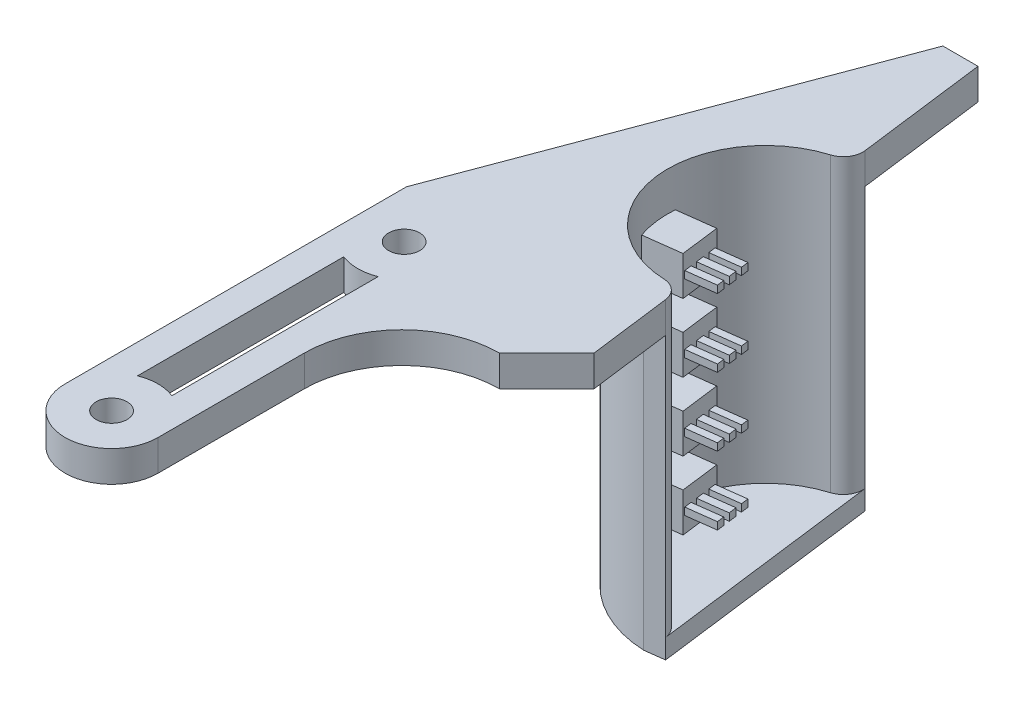
SolidWorks part; units mm, degrees
ref_plane "Alzado" through (0, 0, 0) normal (0, 0, 1) x (1, 0, 0)
ref_plane "Planta" through (0, 0, 0) normal (0, 1, 0) x (1, 0, 0)
ref_plane "Vista lateral" through (0, 0, 0) normal (1, 0, 0) x (0, 0, -1)
sketch "Croquis1" plane through (0, 0, 0) normal (0, 1, 0) x (1, 0, 0)
  line L0 (-12.5, 40) -> (12.5, -40) construction
  line L1 (-12.5, 40) -> (12.5, 40) construction
  line L2 (-12.5, 40) -> (-12.5, -40) construction
  line L3 (-12.5, -40) -> (12.5, -40) construction
  line L4 (12.5, 40) -> (12.5, -40) construction
  line L5 (-12.5, 0) -> (-12.5, -40)
  line L6 (-12.5, -40) -> (-2.975, -40)
  line L7 (-2.975, -40) -> (-2.975, -20)
  line L8 (7.025, -10) -> (12.5, -10)
  line L9 (12.5, -10) -> (12.5, 40)
  line L10 (12.5, 40) -> (2.5, 40)
  line L11 (2.5, 40) -> (-12.5, 0)
  circle A0 centre (-7.7375, -5) radius 1.5875
  circle A1 centre (-7.7375, -35) radius 1.5875
  arc A2 (-2.975, -20) -> (7.025, -10) centre (7.025, -20) cw
  dimension "D5" = 3.175
  dimension "D6" = 3.175
  dimension "D12" = 10
  dimension "D1" = 25
  dimension "D2" = 80
  dimension "D3" = 9.525
  dimension "D4" = 30
  dimension "D7" = 4.7625
  dimension "D8" = 5
  dimension "D9" = 10
  dimension "D10" = 40
  dimension "D11" = 50
extrude "Saliente-Extruir1" add sketch "Croquis1" along normal blind 3.175
sketch "Croquis2" plane through (0, 3.175, 0) normal (0, 1, 0) x (1, 0, 0)
  line L0 (12.5, -10) -> (6.1, 40)
  line L1 (12.5, 40) -> (2.5, 40) construction
  line L2 (6.1, 40) -> (12.5, 40)
  line L3 (12.5, 40) -> (12.5, -10)
  dimension "D1" = 6.4
extrude "Cortar-Extruir1" cut sketch "Croquis2" against normal blind 3.175
sketch "Croquis3" plane through (0, 3.175, 0) normal (0, 1, 0) x (1, 0, 0)
  line L1 (-2.975, -40) -> (-2.975, -20) construction
  line L2 (-12.5, -35) -> (-12.5, -40)
  line L3 (-12.5, -40) -> (-2.975, -40)
  line L4 (-2.975, -40) -> (-2.975, -35)
  line L5 (-9.5, -9.4271) -> (-9.5, -30.5756)
  line L6 (-5.975, -14.8038) -> (-5.975, -30.5756)
  line L7 (-12.5, 0) -> (-12.5, -40) construction
  line L8 (-5.975, -14.8038) -> (-5.975, -9.4271)
  line L22 (7.025, -6) -> (7.9554, -6)
  line L23 (7.9554, -6) -> (3.2646, 30.6468)
  line L24 (3.2646, 30.6468) -> (-8.5, -0.7253)
  line L25 (-8.5, -0.7253) -> (-8.5, -36)
  line L26 (-8.5, -36) -> (-6.975, -36)
  line L27 (-6.975, -36) -> (-6.975, -20)
  line L28 (7.025, -6) -> (7.9554, -6)
  arc A2 (-9.5, -9.4271) -> (-5.975, -9.4271) centre (-7.7375, -5) ccw
  arc A3 (-12.5, -35) -> (-2.975, -35) centre (-7.7375, -35) ccw
  arc A4 (-5.975, -30.5756) -> (-9.5, -30.5756) centre (-7.7375, -35) ccw
  arc A6 (7.025, -6) -> (-6.975, -20) centre (7.025, -20) ccw
  dimension "D1" = 9.53
  dimension "D2" = 3
  dimension "D3" = 3
  dimension "D5" = 4
extrude "Cortar-Extruir3" cut sketch "Croquis3" against normal blind 10 contours A4 L6 L8 A2 L5 | A3 L4 L3 L2
sketch "Croquis5" plane through (0, 3.175, 0) normal (0, 1, 0) x (1, 0, 0)
  line L0 (6.1, 40) -> (12.5, -10) construction
  line L1 (7.025, -10) -> (11.8787, -5.1463)
  line L2 (11.8787, -5.1463) -> (12.5, -10)
  line L3 (12.5, -10) -> (7.025, -10)
  circle A0 centre (9.3, 15) radius 10
  dimension "D1" = 20
  dimension "D2" = 25
  dimension "D3" = 45
extrude "Cortar-Extruir8" cut sketch "Croquis5" against normal blind 10
fillet "Redondeo2" radius 2 2 edges at (8.0304, 1.5875, -24.9191) (10.5696, 1.5875, -5.0809)
sketch "Sketch1" plane through (0, 3.175, 0) normal (0, 1, 0) x (1, 0, 0)
  line L0 (5.8139, 26.4825) -> (7.7977, 26.7364)
  line L2 (8.8184, 3.0097) -> (10.8023, 3.2636)
  arc A0 (6.3949, 24.5687) -> (8.8987, 5.0081) centre (9.3, 15) ccw construction
  arc A1 (6.3949, 24.5687) -> (8.8987, 5.0081) centre (9.3, 15) ccw
  arc A2 (6.3949, 24.5687) -> (7.7977, 26.7364) centre (5.8139, 26.4825) ccw construction
  arc A3 (6.3949, 24.5687) -> (7.7977, 26.7364) centre (5.8139, 26.4825) ccw
  arc A4 (10.8023, 3.2636) -> (8.8987, 5.0081) centre (8.8184, 3.0097) ccw construction
  arc A5 (10.8023, 3.2636) -> (8.8987, 5.0081) centre (8.8184, 3.0097) ccw
  arc A6 (5.8139, 26.4825) -> (5.8139, 26.4825) centre (5.8139, 26.4825) cw
  arc A7 (5.8139, 26.4825) -> (8.8184, 3.0097) centre (9.3, 15) ccw
  arc A8 (8.8184, 3.0097) -> (8.8184, 3.0097) centre (8.8184, 3.0097) cw
  dimension "D1" = 2
extrude "Boss-Extrude1" add sketch "Sketch1" against normal blind 30
sketch "Sketch2" plane through (0, -26.825, 0) normal (0, -1, 0) x (1, 0, 0)
  line L0 (10.8023, -3.2636) -> (7.7977, -26.7364)
  line L2 (5.8139, -26.4825) -> (7.7977, -26.7364)
  line L3 (10.8023, -3.2636) -> (8.8184, -3.0097)
  line L4 (5.8139, -26.4825) -> (7.7977, -26.7364)
  line L5 (10.8023, -3.2636) -> (8.8184, -3.0097)
  arc A4 (7.7977, -26.7364) -> (6.3949, -24.5687) centre (5.8139, -26.4825) ccw
  arc A5 (8.8987, -5.0081) -> (6.3949, -24.5687) centre (9.3, -15) ccw
  arc A6 (8.8987, -5.0081) -> (10.8023, -3.2636) centre (8.8184, -3.0097) ccw
  arc A7 (8.8184, -3.0097) -> (5.8139, -26.4825) centre (9.3, -15) ccw
  arc A11 (8.8184, -3.0097) -> (5.8139, -26.4825) centre (9.3, -15) ccw
  dimension "D1" = 0
extrude "Boss-Extrude2" add sketch "Sketch2" along normal blind 2
sketch "Sketch3" plane through (0, 3.175, 0) normal (0, 1, 0) x (1, 0, 0)
  line L0 (1.2518, 70) -> (-1.34, 70)
  line L1 (2.5, 40) -> (-1.34, 70)
  line L2 (6.1, 40) -> (7.7977, 26.7364) construction
  line L4 (5.0918, 40) -> (5.3981, 37.6073) construction
  line L7 (6.1, 40) -> (2.5, 40) construction
  line L8 (5.0918, 40) -> (2.5, 40)
  line L9 (5.0918, 40) -> (1.2518, 70)
  dimension "D1" = 30
  dimension "D2" = 1
extrude "Boss-Extrude3" [suppressed] add sketch "Sketch3" against normal up to surface (32 mm away)
sketch "Sketch6" [suppressed] plane through (10.0472, 0, -1.286) normal (0.9919, 0, -0.127) x (-0.127, 0, -0.9919)
  line L2 (39.0298, -28.825) -> (69.2746, -28.825) construction
  line L3 (39.0298, -28.825) -> (39.0298, 0) construction
  circle A0 centre (41.5298, -26.325) radius 1.59
  circle A1 centre (46.5298, -26.325) radius 1.59
  circle A2 centre (51.5298, -26.325) radius 1.59
  circle A3 centre (56.5298, -26.325) radius 1.59
  circle A4 centre (61.5298, -26.325) radius 1.59
  circle A5 centre (66.5298, -26.325) radius 1.59
  circle A6 centre (46.5298, -21.825) radius 1.59
  circle A7 centre (51.5298, -21.825) radius 1.59
  circle A8 centre (56.5298, -21.825) radius 1.59
  circle A9 centre (61.5298, -21.825) radius 1.59
  circle A10 centre (66.5298, -21.825) radius 1.59
  circle A11 centre (46.5298, -17.325) radius 1.59
  circle A12 centre (51.5298, -17.325) radius 1.59
  circle A13 centre (56.5298, -17.325) radius 1.59
  circle A14 centre (61.5298, -17.325) radius 1.59
  circle A15 centre (66.5298, -17.325) radius 1.59
  circle A16 centre (46.5298, -12.825) radius 1.59
  circle A17 centre (51.5298, -12.825) radius 1.59
  circle A18 centre (56.5298, -12.825) radius 1.59
  circle A19 centre (61.5298, -12.825) radius 1.59
  circle A20 centre (66.5298, -12.825) radius 1.59
  circle A21 centre (46.5298, -8.325) radius 1.59
  circle A22 centre (51.5298, -8.325) radius 1.59
  circle A23 centre (56.5298, -8.325) radius 1.59
  circle A24 centre (61.5298, -8.325) radius 1.59
  circle A25 centre (66.5298, -8.325) radius 1.59
  circle A26 centre (46.5298, -3.825) radius 1.59
  circle A27 centre (51.5298, -3.825) radius 1.59
  circle A28 centre (56.5298, -3.825) radius 1.59
  circle A29 centre (61.5298, -3.825) radius 1.59
  circle A30 centre (66.5298, -3.825) radius 1.59
  circle A31 centre (46.5298, 0.675) radius 1.59
  circle A32 centre (51.5298, 0.675) radius 1.59
  circle A33 centre (56.5298, 0.675) radius 1.59
  circle A34 centre (61.5298, 0.675) radius 1.59
  circle A35 centre (66.5298, 0.675) radius 1.59
  circle A36 centre (41.5298, -21.825) radius 1.59
  circle A37 centre (41.5298, -17.325) radius 1.59
  circle A38 centre (41.5298, -12.825) radius 1.59
  circle A39 centre (41.5298, -8.325) radius 1.59
  circle A40 centre (41.5298, -3.825) radius 1.59
  circle A41 centre (41.5298, 0.675) radius 1.59
  dimension "D1" = 3.18
  dimension "D2" = 2.5
  dimension "D3" = 2.5
  dimension "D4" = 6
  dimension "D5" = 7
extrude "Boss-Extrude5" [suppressed] add sketch "Sketch6" along normal blind 1
ref_plane "Plane1" through (5.0877, 0, -0.6512) normal (0.9919, 0, -0.127) x (-0.127, 0, -0.9919)
sketch "Sketch7" plane through (5.0877, 0, -0.6512) normal (0.9919, 0, -0.127) x (-0.127, 0, -0.9919)
  line L0 (25.53, -26.825) -> (1.8657, -26.825) construction
  line L1 (11.6978, -25.825) -> (15.6978, -25.825)
  line L2 (11.6978, -25.825) -> (11.6978, -21.825)
  line L3 (11.6978, -21.825) -> (15.6978, -21.825)
  line L4 (15.6978, -25.825) -> (15.6978, -21.825)
  line L5 (11.6978, -25.825) -> (15.6978, -21.825) construction
  line L6 (11.6978, -21.825) -> (15.6978, -25.825) construction
  line L7 (23.558, 3.175) -> (3.8377, 3.175) construction
  point P0 (13.6978, -23.825)
  point P7 (0, 0)
  point P10 (13.6978, 3.175)
  dimension "D1" = 4
  dimension "D2" = 4
  dimension "D3" = 1
extrude "Boss-Extrude6" add sketch "Sketch7" against normal up to surface (3.798 mm away)
sketch "Sketch9" plane through (5.0877, 0, -0.6512) normal (0.9919, 0, -0.127) x (-0.127, 0, -0.9919)
  line L0 (15.5003, -23.45) -> (14.7503, -23.45)
  line L1 (15.5003, -23.45) -> (15.5003, -24.2)
  line L2 (15.5003, -24.2) -> (14.7503, -24.2)
  line L3 (14.7503, -23.45) -> (14.7503, -24.2)
  line L4 (15.5003, -23.45) -> (14.7503, -24.2) construction
  line L5 (15.5003, -24.2) -> (14.7503, -23.45) construction
  line L6 (14.1003, -23.45) -> (13.2954, -23.45)
  line L7 (14.1003, -23.45) -> (14.1003, -24.2)
  line L8 (14.1003, -24.2) -> (13.2954, -24.2)
  line L9 (13.2954, -23.45) -> (13.2954, -24.2)
  line L10 (14.1003, -23.45) -> (13.2954, -24.2) construction
  line L11 (14.1003, -24.2) -> (13.2954, -23.45) construction
  line L12 (12.6454, -23.45) -> (11.8954, -23.45)
  line L13 (12.6454, -23.45) -> (12.6454, -24.2)
  line L14 (12.6454, -24.2) -> (11.8954, -24.2)
  line L15 (11.8954, -23.45) -> (11.8954, -24.2)
  line L16 (12.6454, -23.45) -> (11.8954, -24.2) construction
  line L17 (12.6454, -24.2) -> (11.8954, -23.45) construction
  line L18 (11.6978, -25.825) -> (15.6978, -25.825) construction
  line L19 (15.6978, -25.825) -> (15.6978, -21.825) construction
  point P0 (15.1253, -23.825)
  point P5 (13.6978, -23.825)
  point P10 (12.2704, -23.825)
  point P15 (0, 0)
  point P18 (0, 0)
  point P19 (13.6978, -25.825)
  point P20 (0, 0)
  point P23 (15.6978, -23.825)
  dimension "D1" = 0.75
  dimension "D2" = 0.75
  dimension "D3" = 0.65
  dimension "D4" = 0.65
extrude "Boss-Extrude7" add sketch "Sketch9" along normal blind 3
pattern_linear "LPattern1" count 4 spacing 7 along (0, 1, 0) of "Boss-Extrude7", "Boss-Extrude6"
